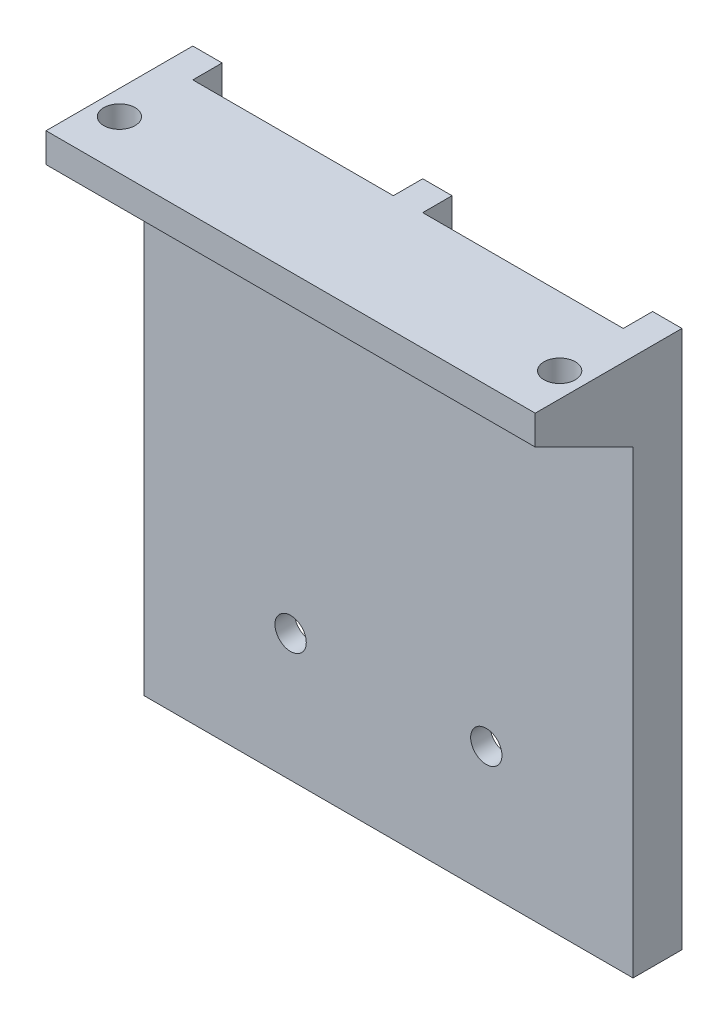
SolidWorks part; units mm, degrees
ref_plane "Front" through (0, 0, 0) normal (0, 0, 1) x (1, 0, 0)
ref_plane "Top" through (0, 0, 0) normal (0, 1, 0) x (1, 0, 0)
ref_plane "Right" through (0, 0, 0) normal (1, 0, 0) x (0, 0, -1)
sketch "草图1" plane through (0, 0, 0) normal (0, 0, 1) x (1, 0, 0)
  line L0 (25, -4.9515) -> (25, -59.9515)
  line L1 (0, -4.9515) -> (-25, -4.9515)
  line L2 (-25, -59.9515) -> (25, -59.9515)
  line L3 (0, -4.9515) -> (25, -4.9515)
  line L4 (-25, -59.9515) -> (-25, -4.9515)
  line L6 (-10, -59.9515) -> (-10, -46.9515) construction
  line L7 (-10, -46.9515) -> (10, -46.9515) construction
  circle A0 centre (10, -46.9515) radius 1.6
  circle A1 centre (-10, -46.9515) radius 1.6
  point P0 (0, 0)
  point P10 (0, 0)
  point P15 (0, 0)
extrude "凸台-拉伸2" add sketch "草图1" against normal blind 2
sketch "草图2" plane through (0, 0, 0) normal (0, 0, 1) x (1, 0, 0)
  line L0 (-25, -4.9515) -> (-25, -7.9515)
  line L3 (-25, -59.9515) -> (-25, -4.9515) construction
  line L4 (-25, -7.9515) -> (25, -7.9515)
  line L5 (25, -4.9515) -> (25, -59.9515) construction
  line L6 (25, -7.9515) -> (25, -4.9515)
  line L7 (25, -4.9515) -> (-25, -4.9515)
extrude "凸台-拉伸3" add sketch "草图2" along normal blind 10
ref_plane "基准面1" through (0, -7.9515, 0) normal (0, -1, 0) x (-1, 0, 0)
sketch "草图3" plane through (0, -7.9515, 0) normal (0, -1, 0) x (-1, 0, 0)
  circle A0 centre (22.5, -5) radius 1.45
  circle A1 centre (-22.5, -5) radius 1.45
  point P4 (0, 0)
  point P5 (0, 0)
extrude "切除-拉伸1" cut sketch "草图3" against normal blind 3
ref_plane "基准面2" through (25, -7.9515, 0) normal (1, 0, 0) x (0, 0, -1)
sketch "草图5" plane through (25, -7.9515, 0) normal (1, 0, 0) x (0, 0, -1)
  line L0 (-10, 0) -> (0, 0)
  line L1 (0, 0) -> (0, -5)
  line L2 (0, -52) -> (0, 0) construction
  line L3 (-10, 0) -> (0, -5)
extrude "凸台-拉伸4" add sketch "草图5" against normal blind 50
sketch "草图7" plane through (0, -7.9515, 0) normal (0, -1, 0) x (-1, 0, 0)
  circle A0 centre (-22.5, -5) radius 2.3
  circle A1 centre (22.5, -5) radius 2.3
sketch "草图8" plane through (0, -7.9515, 0) normal (0, -1, 0) x (-1, 0, 0)
  circle A0 centre (-22.5, -5) radius 1.6
  circle A1 centre (22.5, -5) radius 1.6
extrude "切除-拉伸4" cut sketch "草图8" against normal through all
extrude "切除-拉伸6" cut sketch "草图7" along normal blind 20
sketch "草图10" plane through (0, 0, -2) normal (0, 0, -1) x (-1, 0, 0)
  line L1 (25, -59.9515) -> (-25, -59.9515) construction
  line L2 (0, -59.9515) -> (1.5, -59.9515)
  line L3 (1.5, -59.9515) -> (1.5, -4.9515)
  line L4 (0, -4.9515) -> (25, -4.9515) construction
  line L5 (-25, -59.9515) -> (-22, -59.9515)
  line L6 (-22, -59.9515) -> (-22, -4.9515)
  line L7 (0, -4.9515) -> (-25, -4.9515) construction
  line L8 (-22, -4.9515) -> (-25, -4.9515)
  line L9 (-25, -4.9515) -> (-25, -59.9515)
  line L10 (25, -59.9515) -> (22, -59.9515)
  line L11 (22, -59.9515) -> (22, -4.9515)
  line L12 (22, -4.9515) -> (25, -4.9515)
  line L13 (25, -4.9515) -> (25, -59.9515)
  line L14 (0, -59.9515) -> (-1.5, -59.9515)
  line L15 (-1.5, -59.9515) -> (-1.5, -4.9515)
  line L16 (-1.5, -4.9515) -> (0, -4.9515)
  line M4 (25, -59.9515) -> (25, -4.9515)
  line M5 (25, -4.9515) -> (-25, -4.9515)
  line M7 (-25, -59.9515) -> (25, -59.9515)
extrude "凸台-拉伸5" add sketch "草图10" along normal blind 3 contours L15 L3 M7 M5 | L11 M7 M4 M5 | L9 L5 L6 L8
